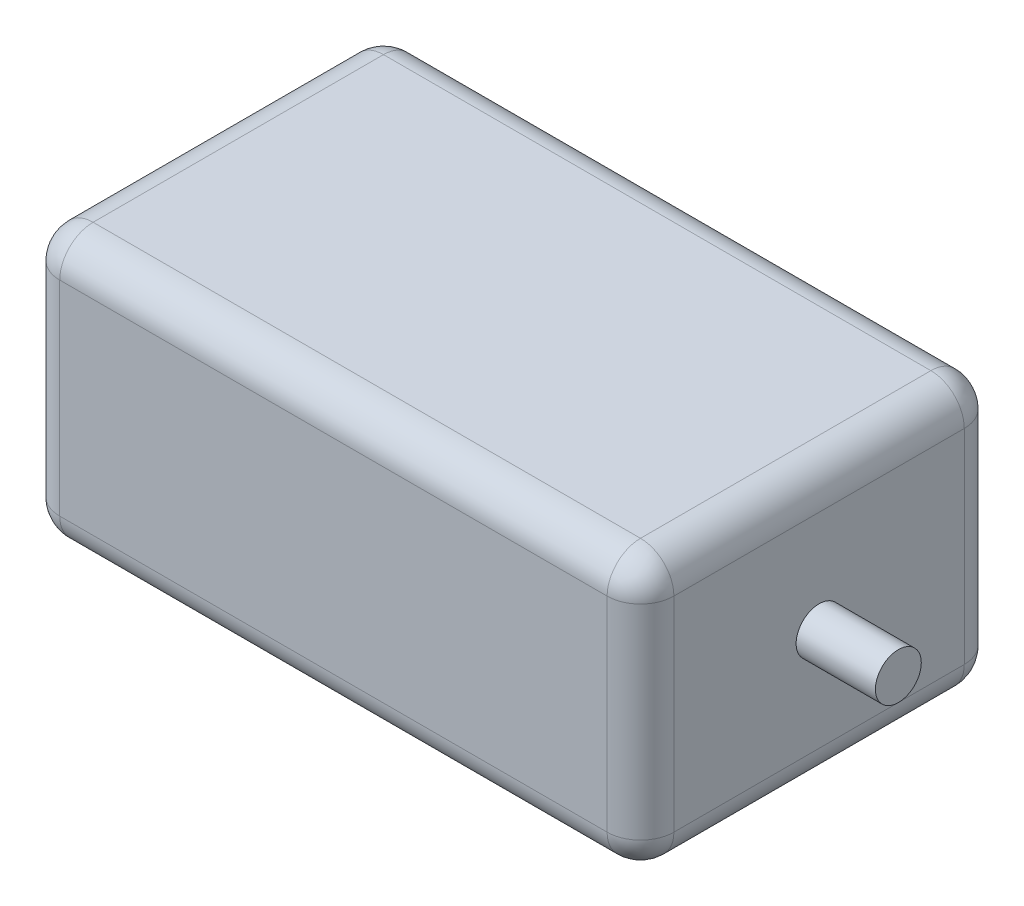
SolidWorks part; units mm, degrees
ref_plane "Front Plane" through (0, 0, 0) normal (0, 0, 1) x (1, 0, 0)
ref_plane "Top Plane" through (0, 0, 0) normal (0, 1, 0) x (1, 0, 0)
ref_plane "Right Plane" through (0, 0, 0) normal (1, 0, 0) x (0, 0, -1)
sketch "Sketch1" plane through (0, 0, 0) normal (0, 1, 0) x (1, 0, 0)
  line L1 (-33.5413, 21.4) -> (40.0587, 21.4)
  line L2 (-33.5413, 21.4) -> (-33.5413, -21.4)
  line L3 (-33.5413, -21.4) -> (40.0587, -21.4)
  line L4 (40.0587, 21.4) -> (40.0587, -21.4)
  line L5 (-33.5413, 21.4) -> (40.0587, -21.4) construction
  line L6 (-33.5413, -21.4) -> (40.0587, 21.4) construction
  point P0 (3.2587, 0)
  dimension "D1" = 42.8
  dimension "D2" = 73.6
extrude "Boss-Extrude1" add sketch "Sketch1" along normal blind 32.5
sketch "Sketch2" plane through (40.0587, 0, 0) normal (1, 0, 0) x (0, 0, -1)
  line L0 (-21.4, 32.5) -> (-21.4, 0) construction
  line L1 (-21.4, 32.5) -> (21.4, 32.5) construction
  circle A0 centre (0, 16.25) radius 2.75
  point P2 (0, 0)
  dimension "D1" = 5.5
  dimension "D3" = 16.25
  dimension "D2" = 21.4
extrude "Boss-Extrude2" add sketch "Sketch2" along normal blind 9.5
fillet "Fillet1" radius 4 12 edges at (40.0587, 16.25, 21.4) (40.0587, 32.5, 0) (40.0587, 16.25, -21.4) (40.0587, 0, 0) (3.2587, 32.5, -21.4) (-33.5413, 32.5, 0) (3.2587, 32.5, 21.4) (-33.5413, 0, 0) (3.2587, 0, -21.4) (3.2587, 0, 21.4) (-33.5413, 16.25, 21.4) (-33.5413, 16.25, -21.4)
